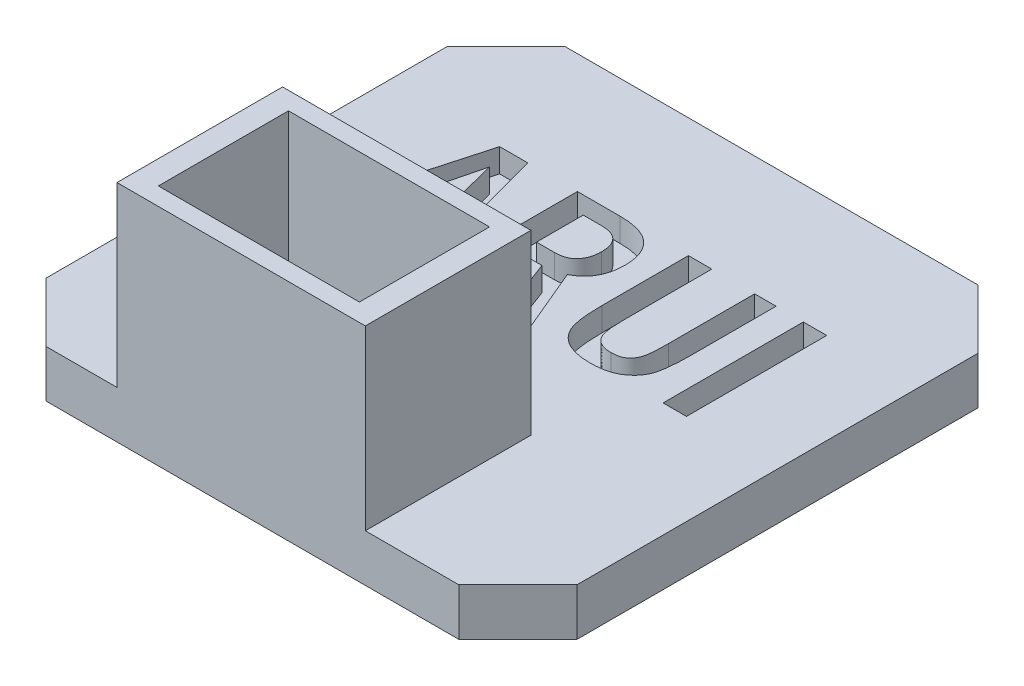
SolidWorks part; units mm, degrees
ref_plane "前基準面" through (0, 0, 0) normal (0, 0, 1) x (1, 0, 0)
ref_plane "上基準面" through (0, 0, 0) normal (0, 1, 0) x (1, 0, 0)
ref_plane "右基準面" through (0, 0, 0) normal (1, 0, 0) x (0, 0, -1)
sketch "草圖1" plane through (0, 0, 0) normal (0, 1, 0) x (1, 0, 0)
  line L1 (-22.45, 21.95) -> (22.45, 21.95)
  line L2 (-22.45, 21.95) -> (-22.45, -21.95)
  line L3 (-22.45, -21.95) -> (22.45, -21.95)
  line L4 (22.45, 21.95) -> (22.45, -21.95)
  line L5 (-22.45, 21.95) -> (22.45, -21.95) construction
  line L6 (-22.45, -21.95) -> (22.45, 21.95) construction
  line L7 (-8.45, -10.95) -> (6.55, -10.95)
  line L8 (-8.45, -10.95) -> (-8.45, -18.95)
  line L9 (-8.45, -18.95) -> (6.55, -18.95)
  line L10 (6.55, -10.95) -> (6.55, -18.95)
  point P0 (0, 0)
  dimension "D1" = 44.9
  dimension "D2" = 43.9
  dimension "D3" = 14
  dimension "D4" = 3
  dimension "D5" = 8
  dimension "D6" = 15
extrude "填料-伸長1" add sketch "草圖1" along normal blind 4
sketch "草圖2" plane through (0, 4, 0) normal (0, 1, 0) x (1, 0, 0)
  line L0 (-8.45, -10.95) -> (-8.45, -18.95) construction
  line L1 (-11.45, -7.95) -> (9.55, -7.95)
  line L2 (-11.45, -7.95) -> (-11.45, -21.95)
  line L3 (-11.45, -21.95) -> (9.55, -21.95)
  line L4 (9.55, -7.95) -> (9.55, -21.95)
  line L5 (6.55, -18.95) -> (6.55, -10.95) construction
  line L6 (-8.45, -18.95) -> (6.55, -18.95) construction
  line L7 (6.55, -10.95) -> (-8.45, -10.95) construction
  dimension "D1" = 3
  dimension "D2" = 3
  dimension "D3" = 3
  dimension "D4" = 3
extrude "填料-伸長2" add sketch "草圖2" along normal blind 15
chamfer "導角1" distance 5 angle 45 4 edges at (22.45, 2, -21.95) (-22.45, 2, 21.95) (22.45, 2, 21.95) (-22.45, 2, -21.95)
sketch "草圖6" plane through (0, 4, 0) normal (0, 1, 0) x (1, 0, 0)
  line L0 (0, 0) -> (17.927, 0) construction
  line L1 (0, 0) -> (-18.2308, 0) construction
  text T0 "ARUI" font "Franklin Gothic Medium Cond" height in points 48
sketch "草圖7" plane through (0, 4, 0) normal (0, 1, 0) x (1, 0, 0)
extrude "除料-伸長2" cut sketch "草圖6" against normal blind 2
sketch "草圖8" plane through (0, 4, 0) normal (0, 1, 0) x (1, 0, 0)
  line L0 (9.55, -21.95) -> (17.45, -21.95) construction
  line L1 (-9.45, -9.45) -> (7.55, -9.45)
  line L2 (-9.45, -9.45) -> (-9.45, -20.45)
  line L3 (-9.45, -20.45) -> (7.55, -20.45)
  line L4 (7.55, -9.45) -> (7.55, -20.45)
  line L5 (-9.45, -9.45) -> (7.55, -20.45) construction
  line L6 (-9.45, -20.45) -> (7.55, -9.45) construction
  line L7 (9.55, -21.95) -> (9.55, -7.95) construction
  point P0 (-0.95, -14.95)
  dimension "D1" = 1.5
  dimension "D2" = 11
  dimension "D3" = 17
  dimension "D4" = 2
extrude "除料-伸長3" cut sketch "草圖8" against normal through all both and the other way through all
